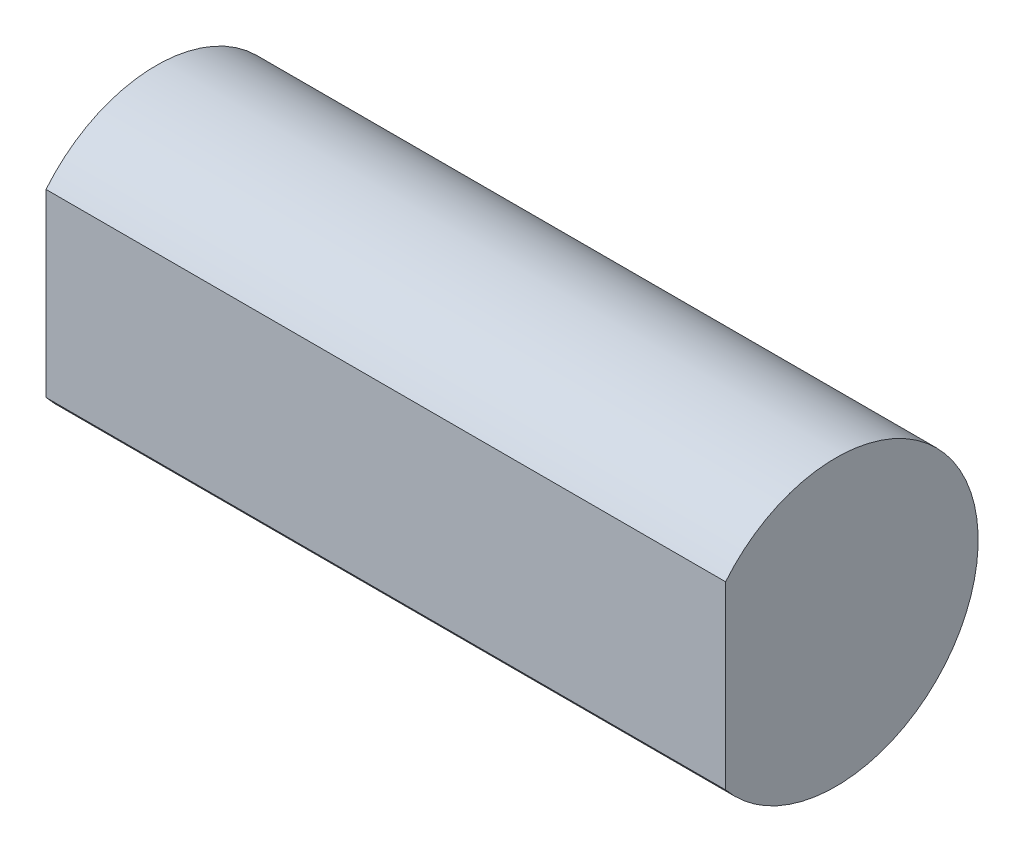
SolidWorks part; units mm, degrees
ref_plane "Alzado" through (0, 0, 0) normal (1, 0, 0) x (0, 1, 0)
ref_plane "Planta" through (0, 0, 0) normal (0, 0, 1) x (0, 1, 0)
ref_plane "Vista lateral" through (0, 0, 0) normal (0, 1, 0) x (-1, 0, 0)
sketch "Croquis1" plane through (0, 0, 0) normal (1, 0, 0) x (0, 1, 0)
  line L0 (2.4527, 3) -> (-2.4527, 3)
  arc A0 (-2.4527, 3) -> (2.4527, 3) centre (0, 0) ccw
  dimension "D1" = 7.75
  dimension "D2" = 3
extrude "Saliente-Extruir1" add sketch "Croquis1" along normal blind 18.5
